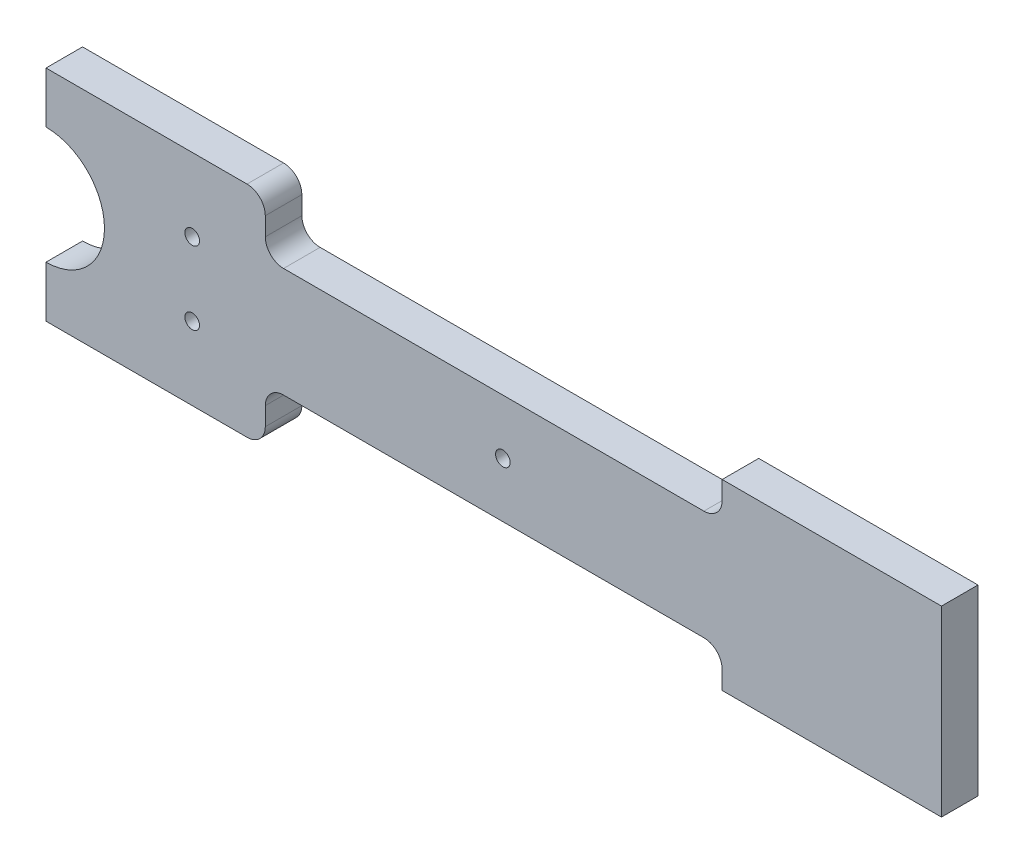
SolidWorks part; units mm, degrees
material "1060 Alloy"
ref_plane "Front Plane" through (0, 0, 0) normal (0, 0, 1) x (1, 0, 0)
ref_plane "Top Plane" through (0, 0, 0) normal (0, 1, 0) x (1, 0, 0)
ref_plane "Right Plane" through (0, 0, 0) normal (1, 0, 0) x (0, 0, -1)
sketch "Sketch1" plane through (0, 0, 0) normal (0, 0, 1) x (1, 0, 0)
  line L0 (245, 5) -> (245, 55)
  line L1 (-60, 0) -> (60, 0)
  line L2 (185, 55) -> (245, 55)
  line L3 (185, 45) -> (185, 55)
  line L4 (60, 0) -> (60, 15)
  line L5 (60, 45) -> (185, 45)
  line L6 (60, 60) -> (60, 45)
  line L7 (60, 15) -> (185, 15)
  line L8 (245, 30) -> (0, 30) construction
  line L9 (-60, 60) -> (60, 60)
  line L10 (0, 0) -> (0, 60) construction
  line L11 (185, 5) -> (245, 5)
  line L12 (-60, 60) -> (-60, 45)
  line L13 (215, 30) -> (215, 5) construction
  line L14 (185, 15) -> (185, 5)
  line L15 (-60, 45) -> (-185, 45)
  line L16 (-185, 45) -> (-185, 55)
  line L17 (-185, 55) -> (-245, 55)
  line L18 (-245, 5) -> (-245, 55)
  line L19 (-185, 5) -> (-245, 5)
  line L20 (-185, 15) -> (-185, 5)
  line L21 (-60, 15) -> (-185, 15)
  line L22 (-60, 0) -> (-60, 15)
  dimension "D1" = 245
  dimension "D2" = 60
  dimension "D3" = 60
  dimension "D4" = 30
  dimension "D5" = 25
  dimension "D6" = 15
extrude "Boss-Extrude1" add sketch "Sketch1" along normal blind 10
sketch "Sketch2" plane through (0, 0, 10) normal (0, 0, 1) x (1, 0, 0)
  line L0 (0, 0) -> (0, 60) construction
  line L1 (-60, 0) -> (60, 0) construction
  line L2 (60, 60) -> (-60, 60) construction
  line L3 (0, 30) -> (245, 30) construction
  line L4 (245, 5) -> (245, 55) construction
  circle A0 centre (40, 20) radius 2
  circle A2 centre (40, 40) radius 2
  circle A3 centre (-40, 40) radius 2
  circle A4 centre (-40, 20) radius 2
  circle A5 centre (0, 30) radius 16
  dimension "D3" = 4
  dimension "D6" = 32
  dimension "D1" = 40
  dimension "D2" = 10
extrude "Cut-Extrude1" cut sketch "Sketch2" against normal through all
fillet "Fillet1" radius 5 12 edges at (-185, 45, 5) (-185, 15, 5) (185, 15, 5) (185, 45, 5) (-60, 45, 5) (-60, 60, 5) (-60, 15, 5) (-60, 0, 5) (60, 45, 5) (60, 60, 5) (60, 15, 5) (60, 0, 5)
sketch "Sketch3" plane through (0, 0, 10) normal (0, 0, 1) x (1, 0, 0)
  line L0 (-245, 30) -> (245, 30) construction
  line L1 (-245, 55) -> (-245, 5) construction
  line L2 (245, 5) -> (245, 55) construction
  line L3 (0, 30) -> (0, 60) construction
  line L4 (55, 60) -> (-55, 60) construction
  circle A0 centre (-125, 30) radius 2
  circle A1 centre (125, 30) radius 2
  dimension "D2" = 4
  dimension "D1" = 125
extrude "Cut-Extrude2" cut sketch "Sketch3" against normal through all
sketch "Sketch4" plane through (0, 0, 0) normal (1, 0, 0) x (0, 0, -1)
  line L1 (-10, 60) -> (0, 60)
  line L2 (-10, 60) -> (-10, 0)
  line L3 (-10, 0) -> (0, 0)
  line L4 (0, 60) -> (0, 0)
extrude "Cut-Extrude3" cut sketch "Sketch4" against normal through all
sketch "Sketch5" plane through (0, 0, 0) normal (-1, 0, 0) x (0, 0, 1)
  line L0 (10, 60) -> (0, 46) construction
  line L1 (0, 14) -> (10, 0) construction
  circle A0 centre (5, 53) radius 2
  circle A1 centre (5, 7) radius 2
  dimension "D1" = 4
extrude "Cut-Extrude4" cut sketch "Sketch5" against normal blind 12
